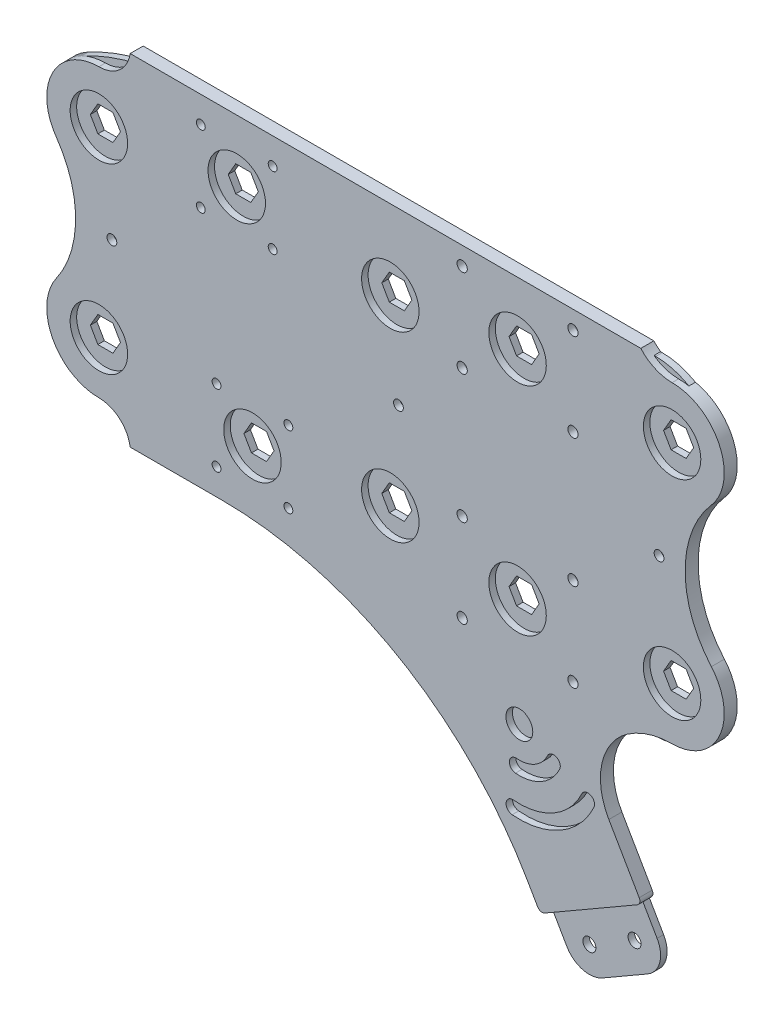
SolidWorks part; units mm, degrees
material "1060 Alloy"
ref_plane "Front Plane" through (0, 0, 0) normal (0, 0, 1) x (1, 0, 0)
ref_plane "Top Plane" through (0, 0, 0) normal (0, 1, 0) x (1, 0, 0)
ref_plane "Right Plane" through (0, 0, 0) normal (1, 0, 0) x (0, 0, -1)
sketch "Sketch1" plane through (0, 0, 0) normal (0, 0, 1) x (1, 0, 0)
  line L9 (183.022, 31.75) -> (225.0336, 31.75)
  line L10 (183.022, 31.75) -> (183.022, 73.7616)
  line L11 (183.022, 73.7616) -> (225.0336, 73.7616)
  line L12 (225.0336, 31.75) -> (225.0336, 73.7616)
  line L13 (183.022, 31.75) -> (225.0336, 73.7616) construction
  line L14 (183.022, 73.7616) -> (225.0336, 31.75) construction
  line L15 (17.8512, 0) -> (50000, 0) construction
  line L16 (46.1727, 31.75) -> (88.1843, 31.75)
  line L17 (46.1727, 31.75) -> (46.1727, 73.7616)
  line L18 (46.1727, 73.7616) -> (88.1843, 73.7616)
  line L19 (88.1843, 31.75) -> (88.1843, 73.7616)
  line L20 (46.1727, 31.75) -> (88.1843, 73.7616) construction
  line L21 (46.1727, 73.7616) -> (88.1843, 31.75) construction
  line L22 (207.694, 59.1058) -> (200.3617, 59.1058)
  line L23 (200.3617, 59.1058) -> (196.6955, 52.7558)
  line L24 (196.6955, 52.7558) -> (200.3617, 46.4058)
  line L25 (200.3617, 46.4058) -> (207.694, 46.4058)
  line L26 (207.694, 46.4058) -> (211.3602, 52.7558)
  line L27 (211.3602, 52.7558) -> (207.694, 59.1058)
  line L28 (74.5108, 52.7558) -> (70.8447, 59.1058)
  line L29 (70.8447, 59.1058) -> (63.5123, 59.1058)
  line L30 (63.5123, 59.1058) -> (59.8461, 52.7558)
  line L31 (59.8461, 52.7558) -> (63.5123, 46.4058)
  line L32 (63.5123, 46.4058) -> (70.8447, 46.4058)
  line L33 (70.8447, 46.4058) -> (74.5108, 52.7558)
  line L34 (3.6662, 50.8) -> (-3.6662, 50.8)
  line L35 (-3.6662, 50.8) -> (-7.3323, 44.45)
  line L36 (-7.3323, 44.45) -> (-3.6662, 38.1)
  line L37 (-3.6662, 38.1) -> (3.6662, 38.1)
  line L38 (3.6662, 38.1) -> (7.3323, 44.45)
  line L39 (7.3323, 44.45) -> (3.6662, 50.8)
  line L40 (282.994, 57.15) -> (275.6617, 57.15)
  line L41 (275.6617, 57.15) -> (271.9955, 50.8)
  line L42 (271.9955, 50.8) -> (275.6617, 44.45)
  line L43 (275.6617, 44.45) -> (282.994, 44.45)
  line L44 (282.994, 44.45) -> (286.6602, 50.8)
  line L45 (286.6602, 50.8) -> (282.994, 57.15)
  line L46 (53.8347, -73.7616) -> (95.8463, -31.75) construction
  line L47 (53.8347, -31.75) -> (95.8463, -73.7616) construction
  line L48 (183.022, -73.7616) -> (225.0336, -31.75) construction
  line L49 (183.022, -31.75) -> (225.0336, -73.7616) construction
  line L50 (286.6602, -50.8) -> (282.994, -57.15)
  line L51 (282.994, -44.45) -> (286.6602, -50.8)
  line L52 (275.6617, -44.45) -> (282.994, -44.45)
  line L53 (271.9955, -50.8) -> (275.6617, -44.45)
  line L54 (275.6617, -57.15) -> (271.9955, -50.8)
  line L55 (282.994, -57.15) -> (275.6617, -57.15)
  line L56 (7.3323, -44.45) -> (3.6662, -50.8)
  line L57 (3.6662, -38.1) -> (7.3323, -44.45)
  line L58 (-3.6662, -38.1) -> (3.6662, -38.1)
  line L59 (-7.3323, -44.45) -> (-3.6662, -38.1)
  line L60 (-3.6662, -50.8) -> (-7.3323, -44.45)
  line L61 (3.6662, -50.8) -> (-3.6662, -50.8)
  line L62 (78.5067, -46.4058) -> (82.1729, -52.7558)
  line L63 (71.1743, -46.4058) -> (78.5067, -46.4058)
  line L64 (67.5082, -52.7558) -> (71.1743, -46.4058)
  line L65 (71.1743, -59.1058) -> (67.5082, -52.7558)
  line L66 (78.5067, -59.1058) -> (71.1743, -59.1058)
  line L67 (82.1729, -52.7558) -> (78.5067, -59.1058)
  line L68 (211.3602, -52.7558) -> (207.694, -59.1058)
  line L69 (207.694, -46.4058) -> (211.3602, -52.7558)
  line L70 (200.3617, -46.4058) -> (207.694, -46.4058)
  line L71 (196.6955, -52.7558) -> (200.3617, -46.4058)
  line L72 (200.3617, -59.1058) -> (196.6955, -52.7558)
  line L73 (207.694, -59.1058) -> (200.3617, -59.1058)
  line L74 (95.8463, -31.75) -> (95.8463, -73.7616)
  line L75 (53.8347, -73.7616) -> (95.8463, -73.7616)
  line L76 (53.8347, -31.75) -> (53.8347, -73.7616)
  line L77 (53.8347, -31.75) -> (95.8463, -31.75)
  line L78 (225.0336, -31.75) -> (225.0336, -73.7616)
  line L79 (183.022, -73.7616) -> (225.0336, -73.7616)
  line L80 (183.022, -31.75) -> (183.022, -73.7616)
  line L81 (183.022, -31.75) -> (225.0336, -31.75)
  line L82 (39.8227, 80.1116) -> (268.1917, 80.1116)
  line L83 (88.1843, 73.7616) -> (183.022, 73.7616) construction
  line L96 (39.8227, -80.1116) -> (131.769, -80.1116)
  line L97 (175.7631, -105.5116) -> (224.8617, -190.5527)
  line L98 (230.7557, -99.1616) -> (268.8557, -165.1527)
  line L99 (242.2102, -195.2013) -> (264.2072, -182.5013)
  line L100 (253.2087, -188.8513) -> (190.4278, -80.1116) construction
  line L101 (131.769, -80.1116) -> (241.7543, -80.1116) construction
  line L102 (230.7557, -99.1616) -> (186.7617, -124.5616) construction
  line L103 (205.8117, -157.5572) -> (249.8057, -132.1572) construction
  line L104 (224.8617, -190.5527) -> (268.8557, -165.1527) construction
  line L105 (197.7602, -118.2116) -> (235.8602, -184.2027) construction
  line L106 (219.7572, -105.5116) -> (257.8572, -171.5027) construction
  line L107 (268.1917, -80.1116) -> (241.7543, -80.1116)
  line L108 (177.0278, 31.3058) -> (231.0278, 74.2058) construction
  line L109 (149.3514, -44.45) -> (145.6852, -50.8)
  line L110 (145.6852, 50.8) -> (138.3528, 50.8)
  line L111 (138.3528, 50.8) -> (134.6867, 44.45)
  line L112 (134.6867, 44.45) -> (138.3528, 38.1)
  line L113 (138.3528, 38.1) -> (145.6852, 38.1)
  line L114 (145.6852, 38.1) -> (149.3514, 44.45)
  line L115 (149.3514, 44.45) -> (145.6852, 50.8)
  line L122 (145.6852, -38.1) -> (149.3514, -44.45)
  line L123 (138.3528, -38.1) -> (145.6852, -38.1)
  line L124 (134.6867, -44.45) -> (138.3528, -38.1)
  line L125 (138.3528, -50.8) -> (134.6867, -44.45)
  line L126 (145.6852, -50.8) -> (138.3528, -50.8)
  line L127 (204.0278, 105.5116) -> (204.0278, 0) construction
  line L129 (180.4117, -113.5631) -> (256.6117, -245.5453) construction
  line L130 (180.4117, -113.5631) -> (224.4057, -88.1631) construction
  line L131 (256.6117, -245.5453) -> (300.6057, -220.1453) construction
  line L132 (224.4057, -88.1631) -> (300.6057, -220.1453) construction
  line L133 (180.4117, -113.5631) -> (300.6057, -220.1453) construction
  line L134 (256.6117, -245.5453) -> (224.4057, -88.1631) construction
  line L135 (28.4347, -54.7116) -> (53.8347, -54.7116)
  line L136 (88.1843, 80.1116) -> (113.5843, 80.1116)
  line L137 (88.1843, 80.1116) -> (88.1843, 54.7116)
  line L138 (88.1843, 54.7116) -> (113.5843, 54.7116)
  line L139 (113.5843, 80.1116) -> (113.5843, 54.7116)
  line L140 (28.4347, -54.7116) -> (28.4347, -80.1116)
  line L141 (28.4347, -80.1116) -> (53.8347, -80.1116)
  line L142 (53.8347, -54.7116) -> (53.8347, -80.1116)
  circle A0 centre (0, 44.45) radius 25.4 construction
  circle A1 centre (67.1785, 52.7558) radius 17.5
  circle A2 centre (204.0278, 52.7558) radius 30
  circle A3 centre (279.3278, 50.8) radius 38.1 construction
  circle A4 centre (0, 44.45) radius 14
  circle A5 centre (67.1785, 52.7558) radius 14
  circle A6 centre (204.0278, 52.7558) radius 14
  circle A7 centre (279.3278, 50.8) radius 14
  circle A8 centre (204.0278, 52.7558) radius 6.35 construction
  circle A9 centre (67.1785, 52.7558) radius 6.35 construction
  circle A10 centre (0, 44.45) radius 6.35 construction
  circle A11 centre (279.3278, 50.8) radius 6.35 construction
  circle A12 centre (279.3278, -50.8) radius 6.35 construction
  circle A13 centre (0, -44.45) radius 6.35 construction
  circle A14 centre (74.8405, -52.7558) radius 6.35 construction
  circle A15 centre (204.0278, -52.7558) radius 6.35 construction
  circle A16 centre (279.3278, -50.8) radius 14
  circle A17 centre (204.0278, -52.7558) radius 14
  circle A18 centre (74.8405, -52.7558) radius 14
  circle A19 centre (0, -44.45) radius 14
  circle A20 centre (279.3278, -50.8) radius 38.1 construction
  circle A21 centre (204.0278, -52.7558) radius 30
  circle A22 centre (74.8405, -52.7558) radius 17.5
  circle A23 centre (0, -44.45) radius 25.4 construction
  circle A26 centre (142.019, 44.45) radius 25.4 construction
  arc A37 (175.7631, -105.5116) -> (131.769, -80.1116) centre (131.769, -130.9116) ccw
  arc A38 (230.7557, -99.1616) -> (241.7543, -80.1116) centre (241.7543, -92.8116) cw
  circle A39 centre (197.7602, -118.2116) radius 3.175
  circle A40 centre (219.7572, -105.5116) radius 3.175
  circle A43 centre (216.8102, -151.2072) radius 3.175
  circle A44 centre (238.8072, -138.5072) radius 3.175
  circle A45 centre (235.8602, -184.2027) radius 3.175
  circle A46 centre (257.8572, -171.5027) radius 3.175
  arc A47 (268.8557, -165.1527) -> (264.2072, -182.5013) centre (257.8572, -171.5027) cw
  arc A48 (224.8617, -190.5527) -> (242.2102, -195.2013) centre (235.8602, -184.2027) ccw
  circle A49 centre (0, 44.45) radius 20.35
  arc A50 (39.8227, 80.1116) -> (-12.2752, 66.6869) centre (39.8227, -27.6901) ccw
  arc A51 (284.0457, 20.8532) -> (268.1917, 80.1116) centre (268.1917, 48.3616) ccw
  arc A52 (284.0457, 20.8532) -> (271.9955, 0) centre (296.0641, 0) ccw
  circle A53 centre (0, -44.45) radius 20.35
  arc A54 (39.8227, -80.1116) -> (-12.2752, -66.6869) centre (39.8227, 27.6901) cw
  arc A55 (-12.2752, 66.6869) -> (-12.8954, 22.5669) centre (0, 44.45) ccw
  arc A56 (284.0457, -20.8532) -> (271.9955, 0) centre (296.0641, 0) cw
  arc A57 (-12.8954, 22.5669) -> (0, 0) centre (-26.1938, 0) cw
  arc A58 (-12.8954, -22.5669) -> (0, 0) centre (-26.1938, 0) ccw
  arc A59 (284.0457, -20.8532) -> (268.1917, -80.1116) centre (268.1917, -48.3616) cw
  circle A60 centre (279.3278, 50.8) radius 20.35
  circle A61 centre (279.3278, -50.8) radius 20.35
  circle A64 centre (67.1785, 52.7558) radius 24.7523 construction
  circle A67 centre (231.0278, 74.2058) radius 2.5
  circle A68 centre (177.0278, 31.3058) radius 2.5
  circle A69 centre (142.019, 44.45) radius 14
  circle A70 centre (142.019, 44.45) radius 6.35 construction
  circle A71 centre (142.019, -44.45) radius 14
  circle A72 centre (142.019, -44.45) radius 25.4 construction
  circle A73 centre (231.0278, -74.2058) radius 2.5
  circle A74 centre (177.0278, -31.3058) radius 2.5
  circle A75 centre (49.676, 70.2583) radius 2.159
  circle A76 centre (84.681, 35.2533) radius 2.159
  circle A77 centre (92.343, -35.2533) radius 2.159
  circle A78 centre (57.338, -70.2583) radius 2.159
  circle A79 centre (177.0278, 74.2058) radius 2.5
  circle A80 centre (231.0278, 31.3058) radius 2.5
  circle A81 centre (231.0278, -31.3058) radius 2.5
  circle A82 centre (177.0278, -74.2058) radius 2.5
  circle A83 centre (49.676, 35.2533) radius 2.159
  circle A84 centre (84.681, 70.2583) radius 2.159
  circle A85 centre (92.343, -70.2583) radius 2.159
  circle A86 centre (57.338, -35.2533) radius 2.159
  arc A87 (-12.2752, -66.6869) -> (-12.8954, -22.5669) centre (0, -44.45) cw
  circle A88 centre (0, 44.45) radius 38.1 construction
  circle A89 centre (0, -44.45) radius 38.1 construction
  point P6 (204.0278, 52.7558)
  point P17 (0, 19.05)
  point P18 (279.3278, 88.9)
  point P28 (279.3278, 12.7)
  point P108 (279.3278, -12.7)
  point P110 (279.3278, -88.9)
  point P111 (0, -19.05)
  point P112 (204.0278, -52.7558)
  point P124 (142.019, 19.05)
  point P171 (216.8102, -151.2072)
  point P174 (232.5732, -196.47)
  point P207 (204.0278, 52.7558)
  point P213 (204.0278, 52.7558)
  point P224 (67.1785, 52.7558)
  point P233 (240.5087, -166.8542)
  dimension "D1" = 50.8
  dimension "D2" = 76.2
  dimension "D4" = 35
  dimension "D5" = 60
  dimension "D9" = 28
  dimension "D10" = 28
  dimension "D12" = 28
  dimension "D7" = 6.35
  dimension "D21" = 6.35
  dimension "D22" = 6.35
  dimension "D23" = 6.35
  dimension "D24" = 12.7
  dimension "D28" = 50.8
  dimension "D29" = 12.7
  dimension "D31" = 6.35
  dimension "D35" = 12.7
  dimension "D34" = 12.7
  dimension "D36" = 31.75
  dimension "D37" = 4.318
  dimension "D38" = 49.5046
  dimension "D41" = 5
  dimension "D42" = 50.8
  dimension "D45" = 4.318
  dimension "D54" = 3.5033
  dimension "D55" = 3.5033
  dimension "D56" = 3.5033
  dimension "D57" = 3.5033
  dimension "D58" = 3.5033
  dimension "D59" = 3.5033
  dimension "D60" = 3.5033
  dimension "D61" = 3.5033
  dimension "D3" = 19.05
  dimension "D6" = 42.0116
  dimension "D8" = 42.0116
  dimension "D11" = 67.69
  dimension "D13" = 75.3
  dimension "D14" = 279.4
  dimension "D15" = 12.7
  dimension "D16" = 12.7
  dimension "D17" = 12.7
  dimension "D18" = 12.7
  dimension "D19" = 12.7
  dimension "D20" = 31.75
  dimension "D25" = 50.8
  dimension "D26" = 30
  dimension "D27" = 76.2
  dimension "D30" = 88.9
  dimension "D32" = 12.7
  dimension "D33" = 12.7
  dimension "D39" = 42.9
  dimension "D40" = 54
  dimension "D43" = 75.3
  dimension "D44" = 19.05
  dimension "D46" = 50.8
  dimension "D47" = 152.4
  dimension "D48" = 12.7
  dimension "D49" = 25.4
  dimension "D50" = 3.5033
  dimension "D51" = 3.5033
  dimension "D52" = 3.5033
  dimension "D53" = 3.5033
  dimension "D62" = 25.4
  dimension "D63" = 75.3
sketch "Sketch2" plane through (0, 0, 0) normal (0, 0, 1) x (1, 0, 0)
  line L0 (-130.0566, 0) -> (174.7434, 0) construction
  line L1 (-199982.1488, 0) -> (250000, 0) construction
  line L2 (-130.0566, 25.4) -> (174.7434, 25.4)
  line L3 (-130.0566, -25.4) -> (174.7434, -25.4)
  arc A0 (-130.0566, 25.4) -> (-130.0566, -25.4) centre (-130.0566, 0) ccw
  arc A1 (174.7434, -25.4) -> (174.7434, 25.4) centre (174.7434, 0) ccw
  point P4 (22.3434, 0)
  point P9 (-155.4566, 0)
  point P10 (200.1434, 0)
  dimension "D1" = 25.4
  dimension "D2" = 355.6
extrude "Boss-Extrude3" add sketch "Sketch1" along normal blind 3.175
sketch "Sketch3" [suppressed] plane through (0, 0, 0) normal (0, 0, 1) x (1, 0, 0)
  line L0 (-3.6662, 50.8) -> (3.6662, 38.1) construction
  line L1 (63.5123, 59.1058) -> (70.8447, 46.4058) construction
  line L2 (138.3528, 50.8) -> (145.6852, 38.1) construction
  line L3 (188.9164, 59.1058) -> (196.2487, 46.4058) construction
  line L4 (256.6064, 57.15) -> (263.9387, 44.45) construction
  line L5 (0, 0) -> (252.9402, 0) construction
  circle A0 centre (0, 44.45) radius 14.2875
  circle A1 centre (67.1785, 52.7558) radius 14.2875
  circle A2 centre (142.019, 44.45) radius 14.2875
  circle A3 centre (192.5825, 52.7558) radius 14.2875
  circle A4 centre (260.2725, 50.8) radius 14.2875
  arc A5 (264.9904, 20.8532) -> (264.9904, -20.8532) centre (277.0088, 0) ccw construction
  circle A6 centre (260.2725, -50.8) radius 14.2875
  circle A7 centre (192.5825, -52.7558) radius 14.2875
  circle A8 centre (142.019, -44.45) radius 14.2875
  circle A9 centre (67.1785, -52.7558) radius 14.2875
  circle A10 centre (0, -44.45) radius 14.2875
  dimension "D1" = 28.575
extrude "Cut-Extrude1" [suppressed] cut sketch "Sketch3" along normal blind 3.175
sketch "Sketch4" plane through (0, 0, 0) normal (0, 0, 1) x (1, 0, 0)
  line L0 (248.4449, -180.6001) -> (-24751.5551, 43120.6701) construction
  line L1 (-14, 76.7058) -> (293.3278, 76.7058) construction
  line L2 (-14, 76.7058) -> (-14, -76.7058) construction
  line L3 (-14, -76.7058) -> (293.3278, -76.7058) construction
  line L4 (293.3278, 76.7058) -> (293.3278, -76.7058) construction
  line L5 (-31.75, 44.45) -> (-31.75, 50044.45) construction
  line L6 (113.6599, -691.382) -> (113.6599, 49308.618) construction
  line L7 (-14, 83.0558) -> (293.3278, 83.0558) construction
  line L8 (-14, -83.0558) -> (293.3278, -83.0558) construction
  line L9 (242.2102, -195.2013) -> (264.2072, -182.5013) construction
  line L10 (202.3718, -157.9492) -> (251.8651, -129.3742) construction
  line L11 (0, 44.45) -> (0, -44.45) construction
  line L12 (279.3278, 50.8) -> (279.3278, -50.8) construction
  line L13 (0, 0) -> (279.3278, 0) construction
  line L14 (-14, -76.7058) -> (-14, -83.0558) construction
  line L15 (-14, -79.8808) -> (293.3278, -79.8808) construction
  line L20 (251.8651, -129.3742) -> (264.5651, -151.3712) construction
  line L21 (264.5651, -151.3712) -> (215.0718, -179.9462) construction
  line L22 (215.0718, -179.9462) -> (202.3718, -157.9492) construction
  line L23 (293.3278, -76.7058) -> (293.3278, -83.0558) construction
  line L24 (202.3718, -157.9492) -> (173.7968, -108.4558) construction
  line L25 (173.7968, -108.4558) -> (223.2901, -79.8808) construction
  line L26 (223.2901, -79.8808) -> (251.8651, -129.3742) construction
  line L27 (180.1468, -119.4543) -> (229.6401, -90.8793) construction
  line L28 (15.24, 83.0558) -> (264.0878, 83.0558)
  line L29 (298.4648, 34.0986) -> (298.4648, -34.0986) construction
  line L30 (-20.775, 29.8363) -> (-20.775, -29.8363) construction
  line L31 (15.24, 83.0558) -> (15.24, -83.0558) construction
  line L32 (15.24, -83.0558) -> (59.9527, -83.0558)
  line L33 (208.7218, -168.9477) -> (215.0718, -179.9462)
  line L34 (215.0718, -179.9462) -> (264.5651, -151.3712)
  line L35 (264.5651, -151.3712) -> (248.5101, -123.563)
  line L36 (204.8935, -105.1668) -> (201.6835, -141.8567) construction
  circle A0 centre (0, 44.45) radius 14
  circle A1 centre (142.019, 44.45) radius 14
  circle A2 centre (279.3278, 50.8) radius 14
  circle A3 centre (279.3278, -50.8) radius 14
  circle A4 centre (142.019, -44.45) radius 14
  circle A5 centre (0, -44.45) radius 14
  circle A6 centre (67.1785, 52.7558) radius 14
  circle A7 centre (204.0278, 52.7558) radius 14
  circle A8 centre (204.0278, -52.7558) radius 14
  circle A9 centre (74.8405, -52.7558) radius 14
  circle A11 centre (0, 44.45) radius 31.75 construction
  circle A12 centre (6.35, 0) radius 2.3813
  circle A13 centre (272.9778, 0) radius 2.3813
  circle A14 centre (145.9778, 0) radius 2.3813
  circle A16 centre (92.343, -70.2583) radius 2.159 construction
  circle A17 centre (57.338, -70.2583) radius 2.159 construction
  circle A18 centre (57.338, -35.2533) radius 2.159 construction
  circle A19 centre (92.343, -35.2533) radius 2.159 construction
  circle A20 centre (177.0278, -74.2058) radius 2.5 construction
  circle A21 centre (231.0278, -74.2058) radius 2.5 construction
  circle A22 centre (231.0278, -31.3058) radius 2.5 construction
  circle A23 centre (177.0278, -31.3058) radius 2.5 construction
  circle A24 centre (231.0278, 31.3058) radius 2.5 construction
  circle A25 centre (231.0278, 74.2058) radius 2.5 construction
  circle A26 centre (177.0278, 31.3058) radius 2.5 construction
  circle A27 centre (177.0278, 74.2058) radius 2.5 construction
  circle A28 centre (49.676, 35.2533) radius 2.159 construction
  circle A29 centre (84.681, 35.2533) radius 2.159 construction
  circle A30 centre (84.681, 70.2583) radius 2.159 construction
  circle A31 centre (49.676, 70.2583) radius 2.159 construction
  circle A38 centre (92.343, -70.2583) radius 2.159
  circle A39 centre (57.338, -70.2583) radius 2.159
  circle A40 centre (57.338, -35.2533) radius 2.159
  circle A41 centre (92.343, -35.2533) radius 2.159
  circle A42 centre (177.0278, -74.2058) radius 2.5
  circle A43 centre (231.0278, -74.2058) radius 2.5
  circle A44 centre (231.0278, -31.3058) radius 2.5
  circle A45 centre (177.0278, -31.3058) radius 2.5
  circle A46 centre (231.0278, 31.3058) radius 2.5
  circle A47 centre (231.0278, 74.2058) radius 2.5
  circle A48 centre (177.0278, 31.3058) radius 2.5
  circle A49 centre (177.0278, 74.2058) radius 2.5
  circle A50 centre (49.676, 35.2533) radius 2.159
  circle A51 centre (84.681, 35.2533) radius 2.159
  circle A52 centre (84.681, 70.2583) radius 2.159
  circle A53 centre (49.676, 70.2583) radius 2.159
  circle A54 centre (0, 44.45) radius 25.4 construction
  circle A55 centre (0, -44.45) radius 25.4 construction
  circle A56 centre (279.3278, 50.8) radius 38.1 construction
  circle A58 centre (279.3278, -50.8) radius 38.1 construction
  circle A62 centre (279.3278, 50.8) radius 25.4 construction
  circle A63 centre (279.3278, -50.8) radius 25.4 construction
  arc A64 (279.3278, 76.2) -> (298.4648, 34.0986) centre (279.3278, 50.8) cw
  arc A65 (298.4648, -34.0986) -> (279.3278, -76.2) centre (279.3278, -50.8) cw
  arc A66 (298.4648, 34.0986) -> (298.4648, -34.0986) centre (337.5362, 0) ccw
  arc A67 (264.0878, 83.0558) -> (279.3278, 76.2) centre (279.3278, 96.5667) ccw
  arc A68 (15.24, 83.0558) -> (0, 69.85) centre (0, 85.2467) cw
  arc A69 (0, 69.85) -> (-20.775, 29.8363) centre (0, 44.45) ccw
  arc A70 (-20.775, 29.8363) -> (-20.775, -29.8363) centre (-63.1906, 0) cw
  arc A71 (-20.775, -29.8363) -> (0, -69.85) centre (0, -44.45) ccw
  arc A72 (0, -69.85) -> (15.24, -83.0558) centre (0, -85.2467) cw
  arc A73 (59.9527, -83.0558) -> (208.7218, -168.9477) centre (59.9527, -254.8395) cw
  arc A78 (279.3278, -76.2) -> (257.5239, -83.0558) centre (279.3278, -114.3) ccw
  arc A79 (257.5239, -83.0558) -> (248.5101, -123.563) centre (275.0849, -108.2201) ccw
  circle A80 centre (204.8935, -105.1668) radius 6.5481
  arc A81 (201.6835, -141.8567) -> (238.2728, -120.7319) centre (204.8935, -105.1668) ccw construction
  arc A82 (201.3991, -145.1082) -> (241.2309, -122.1112) centre (204.8935, -105.1668) ccw
  arc A83 (201.968, -138.6052) -> (235.3147, -119.3525) centre (204.8935, -105.1668) ccw
  arc A84 (201.968, -138.6052) -> (201.3991, -145.1082) centre (201.6835, -141.8567) ccw
  arc A85 (241.2309, -122.1112) -> (235.3147, -119.3525) centre (238.2728, -120.7319) ccw
  arc A86 (203.2885, -123.5117) -> (221.5831, -112.9493) centre (204.8935, -105.1668) ccw construction
  arc A87 (203.004, -126.7632) -> (224.5412, -114.3287) centre (204.8935, -105.1668) ccw
  arc A88 (203.573, -120.2603) -> (218.625, -111.57) centre (204.8935, -105.1668) ccw
  arc A89 (203.573, -120.2603) -> (203.004, -126.7632) centre (203.2885, -123.5117) ccw
  arc A90 (224.5412, -114.3287) -> (218.625, -111.57) centre (221.5831, -112.9493) ccw
  point P100 (253.2087, -188.8513)
  point P118 (223.3085, -137.0625)
  point P124 (227.1185, -143.6617)
  point P138 (279.3278, -76.2)
  point P139 (285.6778, 0)
  point P148 (0, -69.85)
  point P160 (214.101, -121.1147)
  dimension "D1" = 28
  dimension "D2" = 50.8
  dimension "D3" = 76.2
  dimension "D7" = 4.7625
  dimension "D12" = 127
  dimension "D13" = 7.62
  dimension "D19" = 15.24
  dimension "D21" = 38.1
  dimension "D16" = 13.0962
  dimension "D24" = 6.5278
  dimension "D5" = 145.4099
  dimension "D6" = 150
  dimension "D10" = 6.35
  dimension "D11" = 6.35
  dimension "D14" = 25.4
  dimension "D15" = 57.15
  dimension "D17" = 57.15
  dimension "D18" = 6.35
  dimension "D20" = 15.24
  dimension "D22" = 248.8478
  dimension "D23" = 12.7
  dimension "D26" = 6.5278
  dimension "D27" = 35
  dimension "D4" = 6.35
  dimension "D8" = 6.35
  dimension "D9" = 6.35
extrude "Boss-Extrude4" add sketch "Sketch4" along normal blind 6.35 separate body
fillet "Fillet1" radius 2.54 2 edges at (264.5651, -151.3712, 3.175) (215.0718, -179.9462, 3.175)
